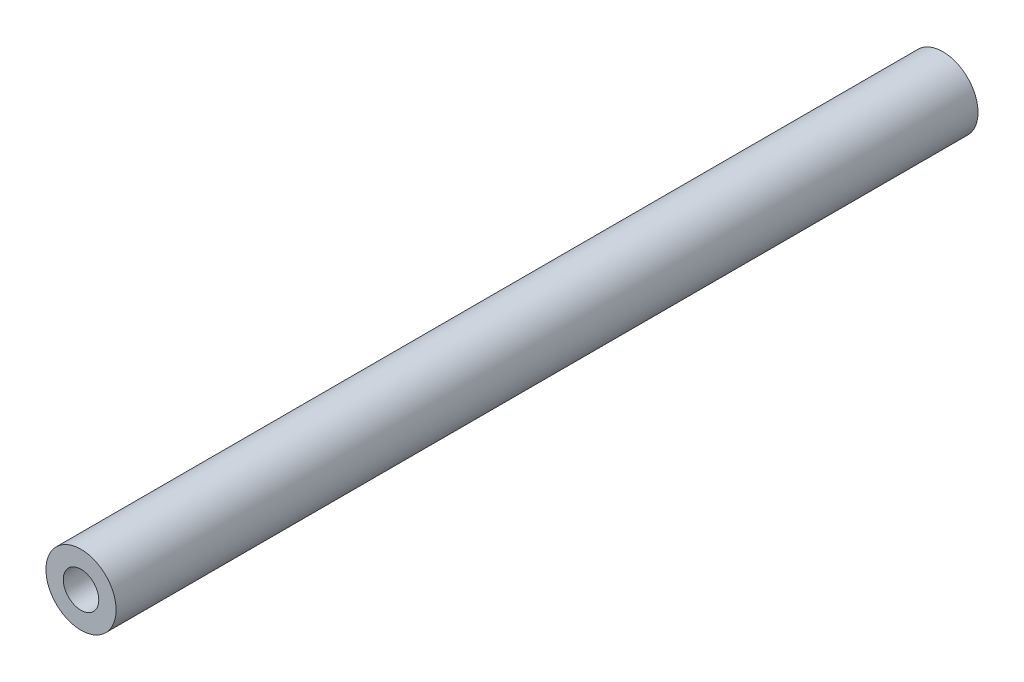
SolidWorks part; units mm, degrees
ref_plane "Front Plane" through (0, 0, 0) normal (0, 0, 1) x (1, 0, 0)
ref_plane "Top Plane" through (0, 0, 0) normal (0, 1, 0) x (1, 0, 0)
ref_plane "Right Plane" through (0, 0, 0) normal (1, 0, 0) x (0, 0, -1)
sketch "Sketch1" plane through (0, 0, 0) normal (0, 0, 1) x (1, 0, 0)
  circle A0 centre (0, 0) radius 25.3273
  circle A1 centre (0, 0) radius 12.8268
extrude "Boss-Extrude1" add sketch "Sketch1" along normal blind 622.3
